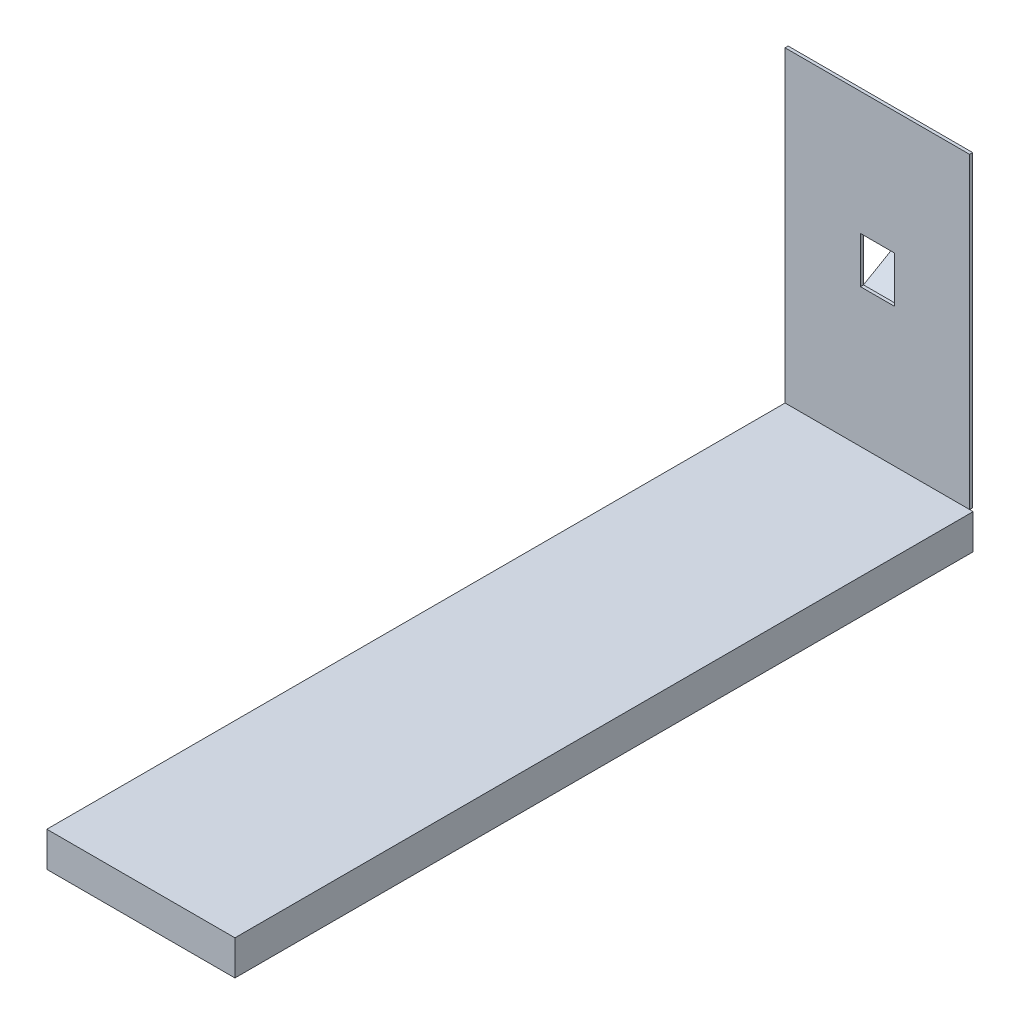
SolidWorks part; units mm, degrees
material "Mahogany"
ref_plane "Front" through (0, 0, 0) normal (0, 0, 1) x (1, 0, 0)
ref_plane "Top" through (0, 0, 0) normal (0, 1, 0) x (1, 0, 0)
ref_plane "Right" through (0, 0, 0) normal (1, 0, 0) x (0, 0, -1)
sketch "Sketch1" plane through (0, 0, 0) normal (0, 0, 1) x (1, 0, 0)
  line L1 (600, -1000) -> (-600, -1000)
  line L2 (600, -1000) -> (600, 1000)
  line L3 (600, 1000) -> (-600, 1000)
  line L4 (-600, -1000) -> (-600, 1000)
  line L5 (600, -1000) -> (-600, 1000) construction
  line L6 (600, 1000) -> (-600, -1000) construction
  point P0 (0, 0)
  dimension "D1" = 2000
  dimension "D2" = 1200
extrude "Boss-Extrude1" add sketch "Sketch1" along normal blind 20
sketch "Sketch3" plane through (0, 0, 20) normal (0, 0, 1) x (1, 0, 0)
  line L0 (-600, -1000) -> (600, -1000) construction
  line L1 (-110, -100) -> (110, -100)
  line L2 (-110, -100) -> (-110, 200)
  line L3 (-110, 200) -> (110, 200)
  line L4 (110, -100) -> (110, 200)
  line L5 (-110, -100) -> (110, 200) construction
  line L6 (-110, 200) -> (110, -100) construction
  point P0 (0, 50)
  dimension "D1" = 300
  dimension "D2" = 220
  dimension "D3" = 900
extrude "Cut-Extrude1" cut sketch "Sketch3" against normal through all
sketch "Sketch4" plane through (0, 0, 0) normal (1, 0, 0) x (0, 0, -1)
  line L0 (0, -100) -> (254, 46.647)
  line L1 (0, -100) -> (0, 200) construction
  line L2 (5, -108.6603) -> (254, 35.1)
  line L3 (5, -108.6603) -> (0, -111.547)
  line L4 (0, -1000) -> (0, 1000) construction
  line L5 (254, 46.647) -> (254, 35.1)
  line L6 (5, -108.6603) -> (259, 37.9867) construction
  line L7 (0, -111.547) -> (0, -100)
  dimension "D1" = 254
  dimension "D2" = 60
  dimension "D3" = 10
extrude "Boss-Extrude2" add sketch "Sketch4" along normal mid plane 220 contours L2 L5 L0 L7 L3
ref_plane "Plane1" through (-600, -1000, 20) normal (1, 0, 0) x (0, 0, -1)
sketch "Sketch7" plane through (0, 0, 20) normal (0, 0, 1) x (1, 0, 0)
  line L1 (-600, -1000) -> (623.0077, -1000)
  line L2 (-600, -1000) -> (-600, -1226.2404)
  line L3 (-600, -1226.2404) -> (623.0077, -1226.2404)
  line L4 (623.0077, -1000) -> (623.0077, -1226.2404)
extrude "Boss-Extrude3" add sketch "Sketch7" along normal blind 4799.5715 separate body
